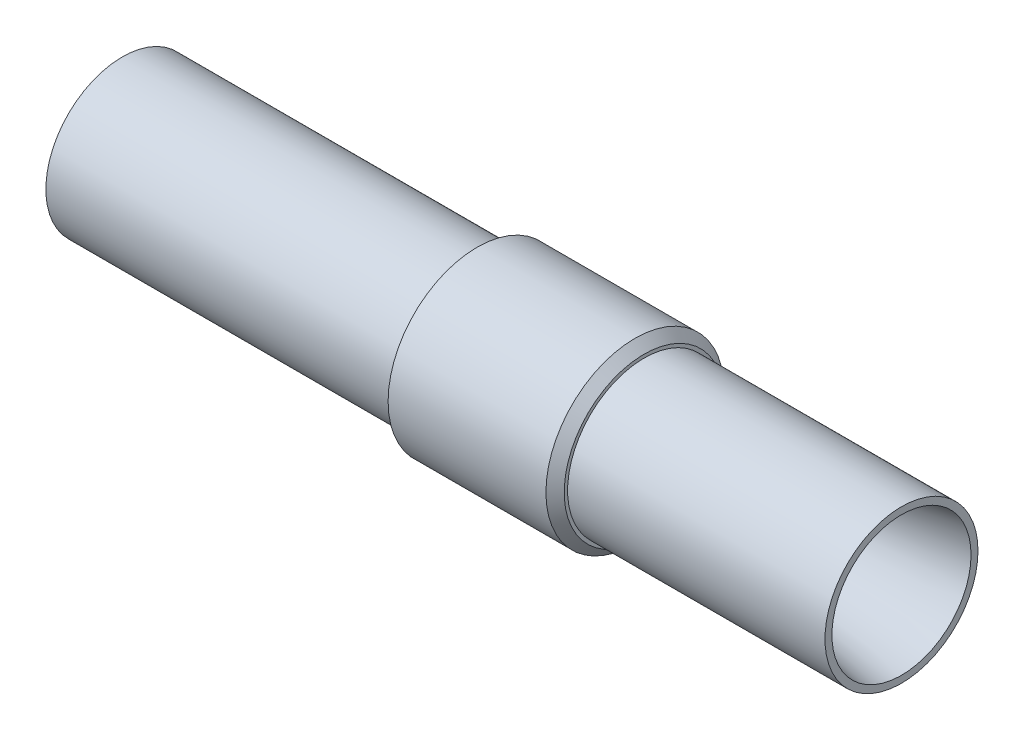
SolidWorks part; units mm, degrees
material "Сталь"
ref_plane "Спереди" through (0, 0, 0) normal (0, 0, 1) x (1, 0, 0)
ref_plane "Сверху" through (0, 0, 0) normal (0, 1, 0) x (1, 0, 0)
ref_plane "Справа" through (0, 0, 0) normal (1, 0, 0) x (0, 0, -1)
sketch "Эскиз1" plane through (0, 0, 0) normal (0, 0, 1) x (1, 0, 0)
  line L0 (0, 0) -> (-291.1314, 0) construction
  line L1 (0, 27.5) -> (-280, 27.5)
  line L2 (0, 27.5) -> (0, 25)
  line L3 (0, 25) -> (-77.5, 12.5)
  line L4 (-77.5, 12.5) -> (-145, 12.5)
  line L5 (-280, 27.5) -> (-280, 25)
  line L6 (-280, 25) -> (-145, 12.5)
  line L7 (0, 25) -> (77.5, 37.5) construction
  line L10 (77.5, -110) -> (77.5, 110) construction
  dimension "D1" = 55
  dimension "D2" = 280
  dimension "D3" = 25
  dimension "D4" = 50
  dimension "D5" = 37.5
  dimension "D6" = 135
revolve "Повернуть1" add sketch "Эскиз1" angle 360 about L0
ref_plane "Плоскость1" through (-152.5, 0, 0) normal (1, 0, 0) x (0, 0, -1)
sketch "Эскиз2" plane through (-152.5, 0, 0) normal (1, 0, 0) x (0, 0, -1)
  circle A0 centre (0, 0) radius 32
  circle A1 centre (0, 0) radius 27.5 construction
  circle A2 centre (0, 0) radius 27.5
  dimension "D1" = 64
extrude "Бобышка-Вытянуть1" add sketch "Эскиз2" along normal blind 60
cosmetic thread "Условное изображение резьбы1" parameters "D2"=57.425
chamfer "Фаска1" distance 3.2875 angle 45 1 edges at (-92.5, 0, -32)
